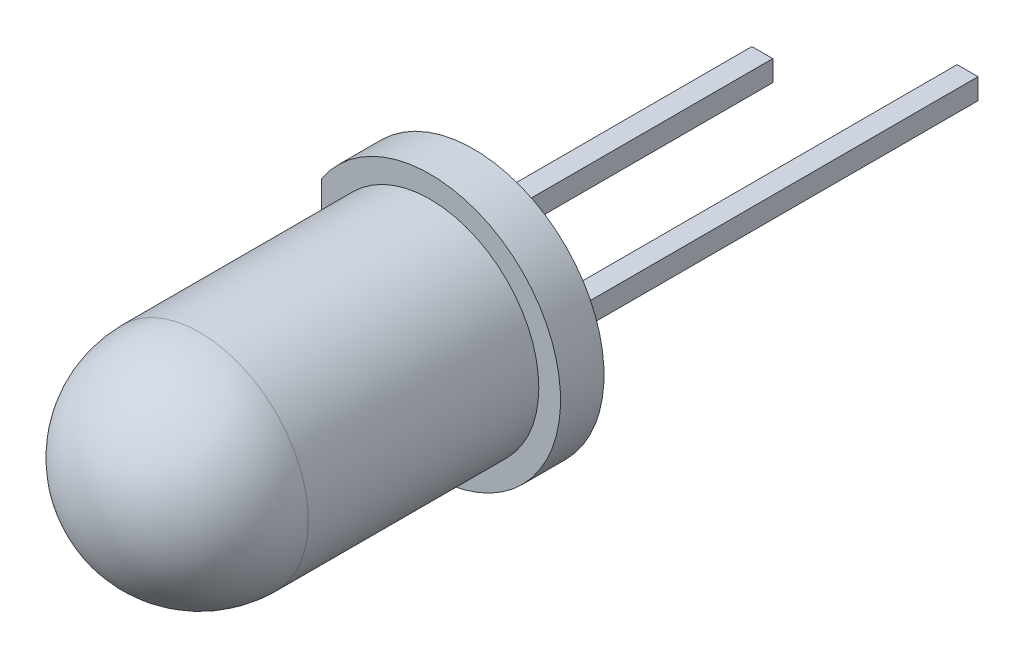
SolidWorks part; units mm, degrees
ref_plane "Plano frontal" through (0, 0, 0) normal (0, 0, 1) x (1, 0, 0)
ref_plane "Plano superior" through (0, 0, 0) normal (0, 1, 0) x (1, 0, 0)
ref_plane "Plano direito" through (0, 0, 0) normal (1, 0, 0) x (0, 0, -1)
sketch "Esboço1" plane through (0, 0, 0) normal (0, 0, 1) x (1, 0, 0)
  circle A0 centre (0, 0) radius 3
  dimension "D1" = 6
extrude "Ressalto-extrusão1" add sketch "Esboço1" along normal blind 1
sketch "Esboço3" plane through (0, 0, 0) normal (1, 0, 0) x (0, 0, -1)
  line L0 (-1, 0) -> (-8.8, 0)
  line L1 (-1, 3) -> (-1, -3) construction
  line L2 (-6.3, 2.5) -> (-1, 2.5)
  line L3 (-1, 0) -> (-1, 2.5)
  arc A0 (-8.8, 0) -> (-6.3, 2.5) centre (-6.3, 0) cw
  dimension "D1" = 2.5
  dimension "D2" = 7.8
revolve "Revolução1" add sketch "Esboço3" angle 360 about L0
sketch "Esboço4" plane through (0, 0, 0) normal (0, 0, -1) x (-1, 0, 0)
  line L0 (2.5, 1.6583) -> (2.5, -1.6583)
  circle A0 centre (0, 0) radius 3 construction
  arc A1 (2.5, -1.6583) -> (2.5, 1.6583) centre (0, 0) ccw
  circle A2 centre (0, 0) radius 2.5 construction
extrude "Corte-extrusão1" cut sketch "Esboço4" against normal up to surface (1 mm away) up to face at (2.5, 0, 1)
sketch "Esboço5" plane through (0, 0, 0) normal (0, 0, -1) x (-1, 0, 0)
  line L0 (-1.12, 0) -> (1.12, 0) construction
  line L1 (-1.6, -0.24) -> (-1.12, -0.24)
  line L2 (-1.6, -0.24) -> (-1.6, 0.24)
  line L3 (-1.6, 0.24) -> (-1.12, 0.24)
  line L4 (-1.12, -0.24) -> (-1.12, 0.24)
  line L5 (1.12, -0.24) -> (1.6, -0.24)
  line L6 (1.12, -0.24) -> (1.12, 0.24)
  line L7 (1.12, 0.24) -> (1.6, 0.24)
  line L8 (1.6, -0.24) -> (1.6, 0.24)
  dimension "D1" = 3.2
  dimension "D2" = 0.48
extrude "Ressalto-extrusão2" add sketch "Esboço5" along normal blind 8 separate body
sketch "Esboço6" plane through (0, 0, -8) normal (0, 0, -1) x (-1, 0, 0)
  line L4 (-1.6, 0.24) -> (-1.6, -0.24)
  line L5 (-1.6, -0.24) -> (-1.12, -0.24)
  line L6 (-1.12, -0.24) -> (-1.12, 0.24)
  line L7 (-1.12, 0.24) -> (-1.6, 0.24)
  line L8 (-1.6, 0.24) -> (-1.6, -0.24)
  line L9 (-1.6, -0.24) -> (-1.12, -0.24)
  line L10 (-1.12, -0.24) -> (-1.12, 0.24)
  line L11 (-1.12, 0.24) -> (-1.6, 0.24)
  dimension "D1" = 0
extrude "Ressalto-extrusão3" add sketch "Esboço6" along normal blind 2 separate body
sketch "Esboço7" plane through (0, 0, 0) normal (0, 1, 0) x (1, 0, 0)
  line L0 (-1.6, 0) -> (-1.6, -3.5)
  line L1 (-1.12, 0) -> (-1.12, -2)
  line L2 (0.02, -2) -> (1.2, -4)
  line L3 (1.2, -4) -> (-1.3, -4)
  line L4 (-1.3, -4) -> (-1.6, -3.5)
  line L5 (-1.12, -2) -> (0.02, -2)
  line L6 (1.6, 0) -> (1.6, -4)
  line L7 (1.6, -4) -> (1.4, -4)
  line L8 (1.4, -4) -> (0.22, -2)
  line L9 (0.22, -2) -> (1.12, -2)
  line L10 (1.12, -2) -> (1.12, 0)
  line L11 (-1.6, 0) -> (-1.12, 0)
  line L12 (1.12, 0) -> (1.6, 0)
  dimension "D1" = 4
  dimension "D2" = 2
  dimension "D3" = 2.8
  dimension "D4" = 0.2
  dimension "D5" = 0.9
  dimension "D6" = 3.5
  dimension "D7" = 2.5
extrude "Corte-extrusão2" cut sketch "Esboço7" against normal mid plane 0.48
sketch "Esboço8" plane through (0, 0, 0) normal (0, 1, 0) x (1, 0, 0)
  line L0 (-1.3, -4) -> (1.2, -4) construction
  line L1 (-1.6, -3.5) -> (-1.3, -4) construction
  line L2 (-1.6, 0) -> (-1.6, -3.5) construction
  line L3 (1.2, -4) -> (0.02, -2) construction
  line L4 (0.02, -2) -> (-1.12, -2) construction
  line L5 (-1.12, -2) -> (-1.12, 0) construction
  line L6 (0.22, -2) -> (1.4, -4) construction
  line L7 (1.12, -2) -> (0.22, -2) construction
  line L8 (1.12, 0) -> (1.12, -2) construction
  line L9 (1.6, -4) -> (1.6, 0) construction
  line L10 (1.4, -4) -> (1.6, -4) construction
  line L11 (-1.12, 0) -> (-1.6, 0) construction
  line L12 (1.6, 0) -> (1.12, 0) construction
  line L13 (-1.3, -4) -> (1.2, -4)
  line L14 (-1.6, -3.5) -> (-1.3, -4)
  line L15 (-1.6, 0) -> (-1.6, -3.5)
  line L16 (1.2, -4) -> (0.02, -2)
  line L17 (0.02, -2) -> (-1.12, -2)
  line L18 (-1.12, -2) -> (-1.12, 0)
  line L19 (0.22, -2) -> (1.4, -4)
  line L20 (1.12, -2) -> (0.22, -2)
  line L21 (1.12, 0) -> (1.12, -2)
  line L22 (1.6, -4) -> (1.6, 0)
  line L23 (1.4, -4) -> (1.6, -4)
  line L24 (-1.12, 0) -> (-1.6, 0)
  line L25 (1.6, 0) -> (1.12, 0)
extrude "Ressalto-extrusão4" add sketch "Esboço8" along normal mid plane 0.48 separate body
combine bodies "Combinar1" operation type add bodies to combine 109 106 104
combine bodies "Combinar2" operation type add bodies to combine 108 105
sketch "Esboço10" plane through (0, 0, 0) normal (0, 1, 0) x (1, 0, 0)
  line L0 (-0.05, -4) -> (-0.05, -3.7)
  line L1 (-1.3, -4) -> (1.2, -4) construction
  line L2 (-0.55, -4) -> (-0.05, -4)
  arc A0 (-0.05, -3.7) -> (-0.55, -4) centre (-0.05, -4.2667) ccw
  dimension "D1" = 0.5
  dimension "D2" = 0.3
revolve "Corte-Revolução1" cut sketch "Esboço10" angle 360 about L0
sketch "Esboço11" plane through (0, 0, 0) normal (0, 1, 0) x (1, 0, 0)
  line L0 (-0.55, -4) -> (-0.05, -4) construction
  line L1 (-0.05, -4) -> (-0.05, -3.7) construction
  line L2 (-0.55, -4) -> (-0.05, -4)
  line L3 (-0.05, -4) -> (-0.05, -3.7)
  arc A0 (-0.05, -3.7) -> (-0.55, -4) centre (-0.05, -4.2667) ccw construction
  arc A1 (-0.05, -3.7) -> (-0.55, -4) centre (-0.05, -4.2667) ccw
revolve "Revolução2" add sketch "Esboço11" angle 360 about L3
combine bodies "Combinar3" operation type add bodies to combine 113 112
sketch "Esboço12" plane through (0, 0, 4) normal (0, 0, 1) x (1, 0, 0)
  circle A0 centre (-0.05, 0) radius 0.2
  arc A1 (0.3886, 0.24) -> (-0.4886, 0.24) centre (-0.05, 0) ccw construction
  dimension "D1" = 0.4
extrude "Corte-extrusão3" cut sketch "Esboço12" against normal blind 0.1
sketch "Esboço13" plane through (0, 0, 0) normal (0, 1, 0) x (1, 0, 0)
  line L0 (1.6, 10) -> (-7.0603, 15)
  line L1 (1.6, 10) -> (1.12, 10) construction
  dimension "D1" = 10
  dimension "D2" = 30
ref_plane "Plano1" through (4.7301, 0, -8.1928) normal (0.5, 0, -0.866) x (-0.866, 0, -0.5)
